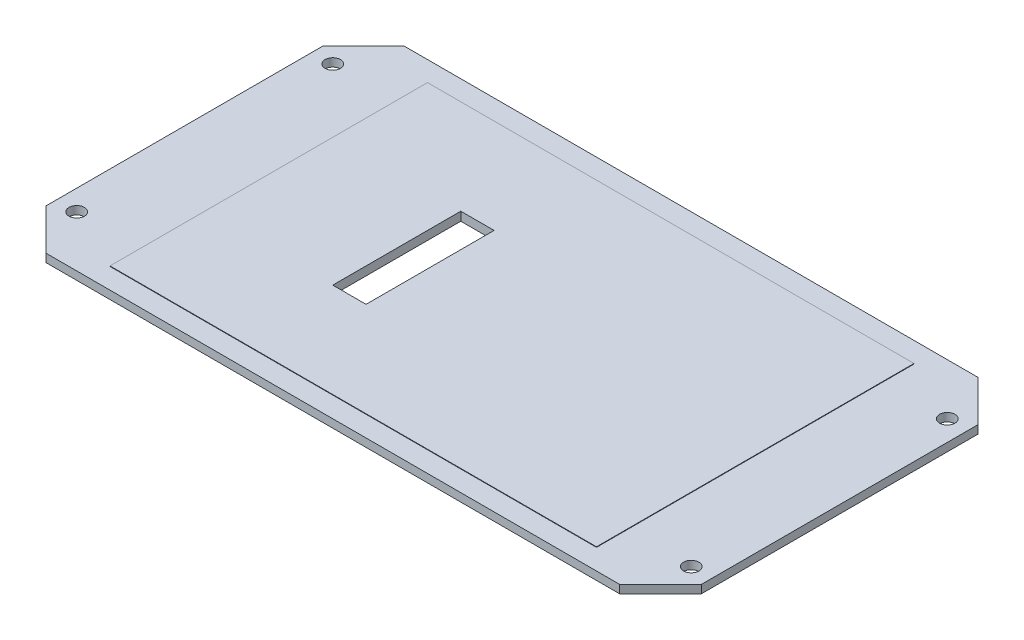
SolidWorks part; units mm, degrees
ref_plane "Front Plane" through (0, 0, 0) normal (0, 0, 1) x (1, 0, 0)
ref_plane "Top Plane" through (0, 0, 0) normal (0, 1, 0) x (1, 0, 0)
ref_plane "Right Plane" through (0, 0, 0) normal (1, 0, 0) x (0, 0, -1)
sketch "Sketch1" plane through (0, -27, 0) normal (0, 1, 0) x (1, 0, 0)
  line L1 (-64, 35) -> (64, 35)
  line L2 (-64, 35) -> (-64, -35)
  line L3 (-64, -35) -> (64, -35)
  line L4 (64, 35) -> (64, -35)
  line L5 (-64, 35) -> (64, -35) construction
  line L6 (-64, -35) -> (64, 35) construction
  point P0 (0, 0)
  dimension "D1" = 70
  dimension "128" = 128
extrude "Boss-Extrude1" add sketch "Sketch1" along normal blind 1.6
chamfer "Chamfer1" distance 8 angle 45 4 edges at (-64, -26.2, -35) (-64, -26.2, 35) (64, -26.2, 35) (64, -26.2, -35)
hole_wizard "Ø3.0 (3) Diameter Hole1" positions "Sketch2" profile "Sketch3" hole size "Ø3.0" standard "ANSI Metric" end condition through all
sketch "Sketch2" plane through (0, -25.4, 0) normal (0, 1, 0) x (1, 0, 0)
  point P0 (-60, -25)
  point P3 (-60, 25)
  point P6 (60, 25)
  point P9 (60, -25)
sketch "Sketch3" plane through (-60, -25.4, 25) normal (1, 0, 0) x (0, 0, 1)
  line L0 (0, 0) -> (0, 1.6)
  line L1 (0, 1.6) -> (1.5, 1.6)
  line L2 (1.5, 1.6) -> (1.5, 0)
  line L5 (1.5, 0) -> (0, 0)
  line L11 (0, -6.35) -> (0, 107.95) construction
  dimension "Thru Hole Dia." = 3
  dimension "Thru Hole Depth" = 1.6
sketch "Sketch4" plane through (0, -25.4, 0) normal (0, 1, 0) x (1, 0, 0)
  line L1 (-47.5, 31) -> (47.5, 31)
  line L2 (-47.5, 31) -> (-47.5, -31)
  line L3 (-47.5, -31) -> (47.5, -31)
  line L4 (47.5, 31) -> (47.5, -31)
  line L5 (-47.5, 31) -> (47.5, -31) construction
  line L6 (-47.5, -31) -> (47.5, 31) construction
  point P0 (0, 0)
  dimension "D1" = 95
  dimension "D2" = 62
extrude "Boss-Extrude2" add sketch "Sketch4" along normal blind 0.1
sketch "Sketch5" plane through (0, -27, 0) normal (0, -1, 0) x (1, 0, 0)
  line L0 (0, 0) -> (-19.25, 0) construction
  line L1 (-22.5, 12.5) -> (-16, 12.5)
  line L2 (-22.5, 12.5) -> (-22.5, -12.5)
  line L3 (-22.5, -12.5) -> (-16, -12.5)
  line L4 (-16, 12.5) -> (-16, -12.5)
  line L5 (-22.5, 12.5) -> (-16, -12.5) construction
  line L6 (-22.5, -12.5) -> (-16, 12.5) construction
  line L7 (-47.5, -31) -> (-47.5, 31) construction
  point P0 (-19.25, 0)
  point P10 (-22.5, 0)
  dimension "D1" = 25
  dimension "D2" = 25
  dimension "D3" = 6.5
extrude "Cut-Extrude1" cut sketch "Sketch5" against normal through all
